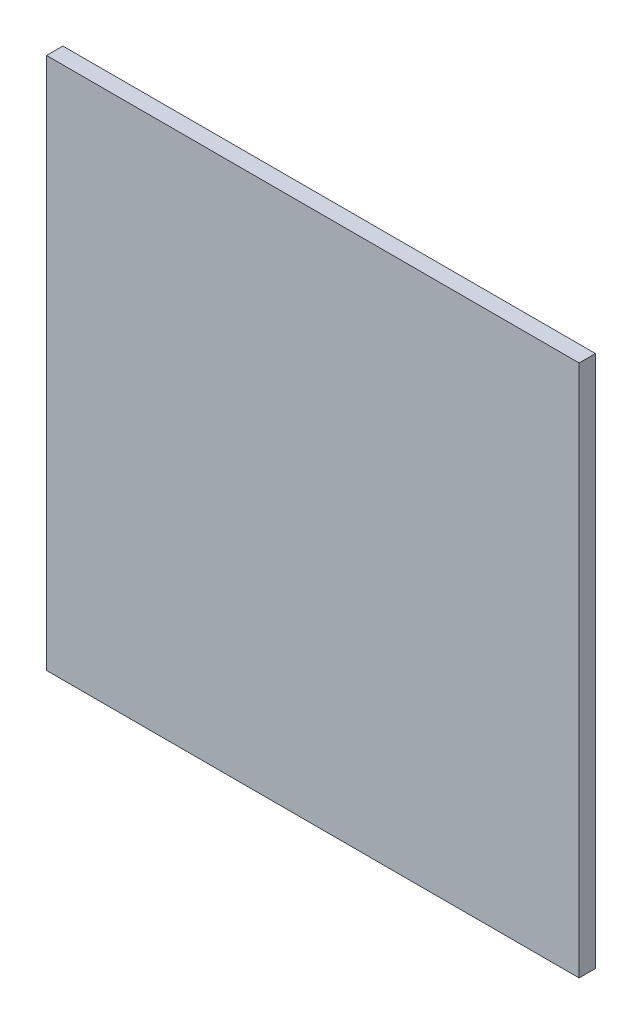
SolidWorks part; units mm, degrees
ref_plane "前视基准面" through (0, 0, 0) normal (0, 0, 1) x (1, 0, 0)
ref_plane "上视基准面" through (0, 0, 0) normal (0, 1, 0) x (1, 0, 0)
ref_plane "右视基准面" through (0, 0, 0) normal (1, 0, 0) x (0, 0, -1)
sketch "草图1" plane through (0, 0, 0) normal (0, 0, 1) x (1, 0, 0)
  line L0 (266.2438, 147.1897) -> (341.2438, 147.1897)
  line L1 (266.2438, 222.1897) -> (341.2438, 222.1897)
  line L2 (266.2438, 222.1897) -> (266.2438, 147.1897)
  line L3 (341.2438, 222.1897) -> (341.2438, 147.1897)
  dimension "D1" = 75
extrude "凸台-拉伸1" add sketch "草图1" along normal blind 2.3
